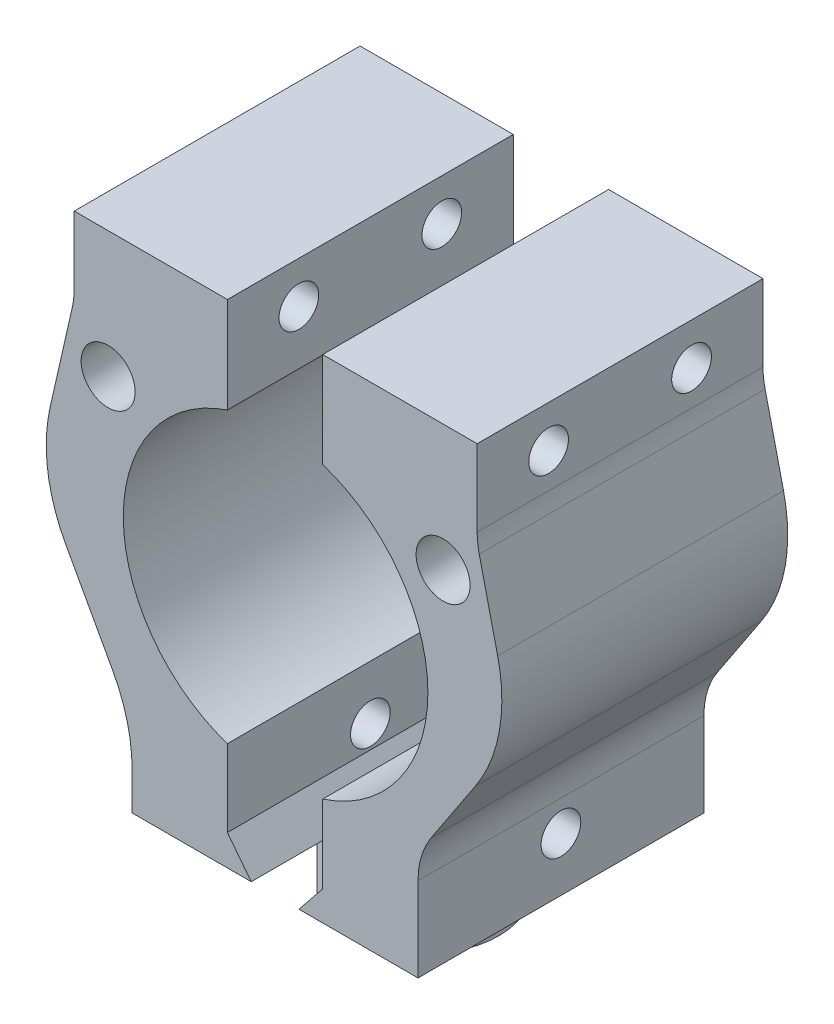
SolidWorks part; units mm, degrees
material "Plain Carbon Steel"
ref_plane "Front Plane" through (0, 0, 0) normal (0, 0, 1) x (1, 0, 0)
ref_plane "Top Plane" through (0, 0, 0) normal (0, 1, 0) x (1, 0, 0)
ref_plane "Right Plane" through (0, 0, 0) normal (1, 0, 0) x (0, 0, -1)
sketch "Sketch1" plane through (0, 0, 0) normal (0, 1, 0) x (1, 0, 0)
  line L0 (0, 4.75) -> (0, -4.75) construction
  line L1 (1.5, 4.5069) -> (1.5, -4.5069)
  line L2 (-1.5, 4.5069) -> (-1.5, -4.5069)
  circle A0 centre (0, 0) radius 4.75
  dimension "D1" = 9.5
  dimension "D2" = 1.5
ref_plane "GroundPlane" through (0, 4.5, 0) normal (0, 1, 0) x (-1, 0, 0)
sketch "Sketch2" plane through (0, 4.5, 0) normal (0, 1, 0) x (-1, 0, 0)
  line L0 (0, 7.5) -> (6.4952, -3.75) construction
  line L1 (0, 7.5) -> (0, -7.5) construction
  line L2 (0, 12.7) -> (0, -12.7) construction
  line L3 (0, 7.5) -> (-6.4952, -3.75) construction
  line L4 (-9.2393, -11.2686) -> (9.8107, -11.2686) construction
  line L5 (-9.2393, -11.2686) -> (-9.2393, -30.3186) construction
  line L6 (-9.2393, -30.3186) -> (9.8107, -30.3186) construction
  line L7 (9.8107, -11.2686) -> (9.8107, -30.3186) construction
  line L8 (-6.4952, -3.75) -> (6.4952, -3.75) construction
  line L9 (0, -7.5) -> (6.4952, 3.75) construction
  line L10 (6.4952, 3.75) -> (-6.4952, 3.75) construction
  line L11 (-6.4952, 3.75) -> (0, -7.5) construction
  line L12 (3, -8.6561) -> (3, 9.3439)
  line L13 (3, -8.6561) -> (15, -8.6561)
  line L14 (3, 9.3439) -> (15, 9.3439)
  line L15 (15, 9.3439) -> (15, -8.6561)
  line L16 (-3, -8.6561) -> (-3, 9.3439)
  line L17 (-3, -8.6561) -> (-15, -8.6561)
  line L18 (-3, 9.3439) -> (-15, 9.3439)
  line L19 (-15, 9.3439) -> (-15, -8.6561)
  circle A0 centre (0, 0) radius 7.5 construction
  dimension "D1" = 15
  dimension "D2" = 30
  dimension "D3" = 25.4
  dimension "D4" = 19.05
  dimension "D5" = 19.05
  dimension "D6" = 30
  dimension "D7" = 30
  dimension "D8" = 3
  dimension "D9" = 18
  dimension "D10" = 12
ref_plane "TopPlane" through (0, 36.25, 0) normal (0, 1, 0) x (-1, 0, 0)
extrude "Extrude1" add sketch "Sketch2" along normal blind 31.75
extrude "Extrude2" add sketch "Sketch1" along normal blind 4.5 contours L1 A0 | L2 A0
sketch "Sketch4" plane through (0, 0, 9.3439) normal (0, 0, 1) x (1, 0, 0)
  line L0 (-14.9586, 36.25) -> (15.0262, 4.5) construction
  line L1 (9.9, 36.25) -> (-9.9, 36.25) construction
  line L2 (9.9, 4.5) -> (-9.9, 4.5) construction
  line L3 (15.0262, 36.25) -> (-14.9586, 4.5) construction
  circle A0 centre (0.0338, 20.375) radius 9.5885
  point P8 (0.0338, 20.375)
  dimension "D1" = 19.177
extrude "Magnet Cavity" cut sketch "Sketch4" against normal through all
sketch "Sketch6" plane through (15, 0, 0) normal (1, 0, 0) x (0, 0, -1)
  line L0 (-9.3439, 36.25) -> (-9.3439, 4.5) construction
  line L1 (-9.3439, 20.375) -> (8.6561, 20.375) construction
  line L2 (8.6561, 36.25) -> (8.6561, 4.5) construction
  line L3 (-0.3439, 36.25) -> (-0.3439, 4.5) construction
  line L4 (-9.3439, 36.25) -> (8.6561, 36.25) construction
  line L5 (-9.3439, 4.5) -> (8.6561, 4.5) construction
  line L6 (-0.3439, 36.25) -> (-9.3439, 29.4932) construction
  point P12 (-4.8439, 32.8716)
  point P15 (4.1561, 32.8716)
  point P16 (4.1561, 7.8784)
  point P17 (-4.8439, 7.8784)
  point P18 (-0.3439, 32.8716)
  point P19 (-0.3439, 7.8784)
sketch "Mount Hole circle" plane through (0, 0, 9.3439) normal (0, 0, 1) x (1, 0, 0)
  line L0 (0.0338, 20.375) -> (0.0338, 33.125) construction
  line L1 (0.0338, 20.375) -> (10.5793, 27.5412) construction
  line L2 (0.0338, 20.375) -> (-10.5117, 27.5412) construction
  circle A0 centre (0.0338, 20.375) radius 12.75 construction
  dimension "D1" = 25.5
  dimension "D2" = 55.802
sketch "Sketch14" plane through (0, 4.5, 0) normal (0, 1, 0) x (-1, 0, 0)
  point P0 (6.4952, 3.75)
  point P1 (-6.4952, 3.75)
  point P3 (0, -7.5)
sketch "Sketch16" plane through (0, 4.5, 0) normal (0, 1, 0) x (-1, 0, 0)
  point P0 (6.4952, 3.75)
  point P1 (-6.4952, 3.75)
  point P3 (0, -7.5)
hole_wizard "M3x0.5 Tapped Hole1" positions "3DSketch3" profile "Sketch18" tap size "M3x0.5" standard "Ansi Metric" end condition through all
sketch3d "3DSketch3"
  point P0 (15, 32.8716, 4.8439)
  point P3 (15, 32.8716, -4.1561)
  point P6 (15, 7.8784, 0.3439)
sketch "Sketch18" plane through (15, 32.8716, 4.8439) normal (0, 1, 0) x (0, 0, -1)
  line L0 (0, 0) -> (0, 30)
  line L1 (0, 30) -> (1.25, 30)
  line L2 (1.25, 30) -> (1.25, 0)
  line L5 (1.25, 0) -> (0, 0)
  line L11 (0, -6.35) -> (0, 107.95) construction
  dimension "Thru Tap Drill Dia." = 2.5
  dimension "Thru Tap Drill Depth" = 30
cosmetic thread "Hole Thread6" parameters "D2"=3
cosmetic thread "Hole Thread7" parameters "D2"=3
cosmetic thread "Hole Thread8" parameters "D2"=3
hole_wizard "M2x0.4 Tapped Hole2" positions "3DSketch8" profile "Sketch23" tap size "M2x0.4" standard "Ansi Metric"
sketch3d "3DSketch8"
  point P9 (-6.4952, 4.5, 3.75)
  point P11 (6.4952, 4.5, 3.75)
sketch "Sketch23" plane through (-6.4952, 4.5, 3.75) normal (1, 0, 0) x (0, 0, -1)
  line L0 (0, 0) -> (0, 6.4807)
  line L1 (0, 6.4807) -> (0.8, 6)
  line L2 (0.8, 6) -> (0.8, 0)
  line L5 (0.8, 0) -> (0, 0)
  line L10 (0, 6.4807) -> (-0.8, 6) construction
  line L11 (0, -6.35) -> (0, 107.95) construction
  dimension "Tap Drill Dia." = 1.6
  dimension "Tap Drill Depth" = 6
  dimension "Drill Angle" = 118
cosmetic thread "Hole Thread16" parameters "D1"=4, "D2"=2
cosmetic thread "Hole Thread17" parameters "D1"=4, "D2"=2
hole_wizard "M3 Clearance Hole1" positions "3DSketch9" profile "Sketch24" hole size "M3" standard "Ansi Metric"
sketch3d "3DSketch9"
  point P0 (-10.5117, 27.5412, 9.3439)
  point P3 (10.5793, 27.5412, 9.3439)
sketch "Sketch24" plane through (-10.5117, 27.5412, 9.3439) normal (1, 0, 0) x (0, -1, 0)
  line L0 (0, 0) -> (0, 19.0215)
  line L1 (0, 19.0215) -> (1.7, 18)
  line L2 (1.7, 18) -> (1.7, 0)
  line L5 (1.7, 0) -> (0, 0)
  line L10 (0, 19.0215) -> (-1.7, 18) construction
  line L11 (0, -6.35) -> (0, 107.95) construction
  dimension "Hole Dia." = 3.4
  dimension "Hole Depth" = 18
  dimension "Drill Angle" = 118
sketch "Trim Sketch" plane through (0, 0, 9.3439) normal (0, 0, 1) x (1, 0, 0)
  line L0 (9, 4.5) -> (9, 9.8054)
  line L1 (3, 4.5) -> (15, 4.5) construction
  line L2 (9.8306, 12.5652) -> (12.619, 16.7778)
  line L3 (15, 36.25) -> (15, 4.5) construction
  line L4 (14.0173, 24.5754) -> (12.8557, 29.5406)
  line L5 (12.7242, 30.6796) -> (12.7242, 35.4973)
  line L6 (12.7242, 35.4973) -> (3, 35.4973)
  line L7 (3, 36.25) -> (3, 29.4932) construction
  line L8 (0.0338, 33.125) -> (0, 0) construction
  line L9 (-8.9908, 4.5183) -> (-8.98, 9.8237)
  line L10 (-9.805, 12.5852) -> (-12.5848, 16.8035)
  line L11 (-13.9672, 24.6039) -> (-12.7954, 29.5667)
  line L12 (-12.6616, 30.7055) -> (-12.6518, 35.5232)
  line L13 (-12.6518, 35.5232) -> (-3, 35.5232)
  line L14 (-3, 36.25) -> (-3, 29.4709) construction
  circle A0 centre (0.0338, 20.375) radius 12.75 construction
  arc A1 (12.8557, 29.5406) -> (12.7242, 30.6796) centre (17.7242, 30.6796) cw
  arc A2 (12.619, 16.7778) -> (14.0173, 24.5754) centre (4.2802, 22.2973) ccw
  arc A3 (9.8306, 12.5652) -> (9, 9.8054) centre (14, 9.8054) ccw
  arc A4 (-9.805, 12.5852) -> (-8.98, 9.8237) centre (-13.98, 9.8339) cw
  arc A5 (-12.5848, 16.8035) -> (-13.9672, 24.6039) centre (-4.2348, 22.306) cw
  arc A6 (-12.7954, 29.5667) -> (-12.6616, 30.7055) centre (-17.6616, 30.7157) ccw
  point P18 (15, 20.375)
  point P21 (9, 11.3103)
  line M2 (3, 36.25) -> (3, 29.4932)
  line M5 (3, 4.5) -> (15, 4.5)
  line M6 (15, 4.5) -> (15, 36.25)
  line M7 (15, 36.25) -> (3, 36.25)
  dimension "D1" = 5
  dimension "D2" = 10
  dimension "D3" = 5
extrude "Extrude3" cut sketch "Trim Sketch" along direction (0, 0, -1) on the side against the normal through all contours L2 A3 L0 L6 L5 A1 L4 A2 M5 M6 M7 M2
sketch "Sketch26" plane through (0, 0, 9.3439) normal (0, 0, 1) x (1, 0, 0)
  line L0 (1.5, 4.5) -> (3, 6.36)
  line L1 (3, 11.2568) -> (3, 4.5) construction
  line L2 (1.5, 4.5) -> (3, 4.5)
  line L3 (3, 4.5) -> (3, 6.36)
extrude "Extrude4" add sketch "Sketch26" against normal up to surface (18 mm away) up to face at (12.2793, 27.5412, -8.6561)
sketch "Sketch27" plane through (0, 0, 9.3439) normal (0, 0, 1) x (1, 0, 0)
  line L0 (-14.1566, 24.0762) -> (-12.771, 30.1568)
  line L1 (-15, 36.25) -> (-15, 4.5) construction
  line L2 (-12.646, 31.2677) -> (-12.646, 35.4975)
  line L3 (-12.646, 35.4975) -> (-3, 35.4975)
  line L4 (-3, 36.25) -> (-3, 29.4709) construction
  line L6 (-3, 9.4328) -> (-9, 9.4328) construction
  line L7 (-3, 11.2791) -> (-3, 4.5) construction
  line L8 (-13.1749, 17.0465) -> (-10.2317, 11.679)
  line L9 (-9, 6.871) -> (-9, 4.5)
  arc A0 (-12.771, 30.1568) -> (-12.646, 31.2677) centre (-17.646, 31.2677) ccw
  arc A1 (-13.1749, 17.0465) -> (-14.1566, 24.0762) centre (-4.4065, 21.8544) cw
  arc A2 (-9, 6.871) -> (-10.2317, 11.679) centre (-19, 6.871) ccw
  point P17 (-15, 20.375)
  line M4 (-3, 29.4709) -> (-3, 36.25)
  line M5 (-3, 36.25) -> (-15, 36.25)
  line M6 (-15, 36.25) -> (-15, 4.5)
  line M7 (-15, 4.5) -> (-3, 4.5)
  dimension "D2" = 5
  dimension "D3" = 10
  dimension "D1" = 6
extrude "Extrude5" cut sketch "Sketch27" along direction (0, 0, -1) on the side against the normal through all contours L9 A2 L8 A1 L0 A0 L2 L3 M4 M5 M6 M7
sketch "Sketch28" plane through (0, 0, 9.3439) normal (0, 0, 1) x (1, 0, 0)
  line L0 (-1.5, 4.5) -> (-3, 6.4338)
  line L1 (-3, 11.2791) -> (-3, 4.5) construction
  line L2 (-3, 6.4338) -> (-3, 4.5)
  line L3 (-3, 4.5) -> (-1.5, 4.5)
extrude "Extrude6" add sketch "Sketch28" against normal up to surface (18 mm away) up to face at (-8.8117, 27.5412, -8.6561)
